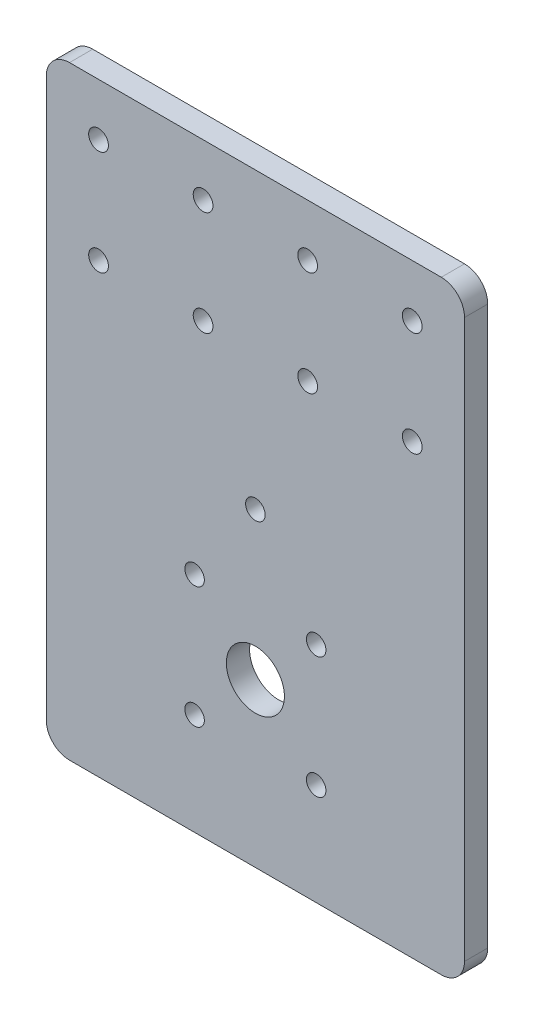
SolidWorks part; units mm, degrees
ref_plane "Front Plane" through (0, 0, 0) normal (0, 0, 1) x (1, 0, 0)
ref_plane "Top Plane" through (0, 0, 0) normal (0, 1, 0) x (1, 0, 0)
ref_plane "Right Plane" through (0, 0, 0) normal (1, 0, 0) x (0, 0, -1)
sketch "Sketch1" plane through (0, 0, 0) normal (0, 0, 1) x (1, 0, 0)
  line L0 (0, 0) -> (37, 0) construction
  line L1 (0, 0) -> (26.163, 26.163) construction
  line L2 (0, 0) -> (0, 63.5) construction
  line L3 (-66.1167, 190) -> (94.9569, 190) construction
  line L4 (0, 0) -> (0, -70) construction
  line L7 (-80, -70) -> (80, -70)
  line L9 (90, -60) -> (90, 180)
  line L10 (80, 190) -> (-80, 190)
  line L11 (-90, 180) -> (-90, -60)
  line L12 (-80, 167.5) -> (80, 167.5) construction
  line L13 (-80, 122.5) -> (80, 122.5) construction
  line L14 (-67.5, 177.3414) -> (-67.5, 115.1625) construction
  circle A0 centre (0, 0) radius 37 construction
  circle A2 centre (26.163, 26.163) radius 4.2
  circle A3 centre (26.163, -26.163) radius 4.2
  circle A4 centre (-26.163, -26.163) radius 4.2
  circle A5 centre (-26.163, 26.163) radius 4.2
  circle A6 centre (0, 63.5) radius 4.2
  arc A7 (90, -60) -> (80, -70) centre (80, -60) cw
  arc A8 (-80, -70) -> (-90, -60) centre (-80, -60) cw
  arc A9 (-90, 180) -> (-80, 190) centre (-80, 180) cw
  arc A10 (80, 190) -> (90, 180) centre (80, 180) cw
  circle A11 centre (-67.5, 167.5) radius 4.25
  circle A12 centre (-67.5, 122.5) radius 4.25
  circle A13 centre (-22.5, 122.5) radius 4.25
  circle A14 centre (-22.5, 167.5) radius 4.25
  circle A15 centre (22.5, 122.5) radius 4.25
  circle A16 centre (22.5, 167.5) radius 4.25
  circle A17 centre (67.5, 122.5) radius 4.25
  circle A18 centre (67.5, 167.5) radius 4.25
  circle A20 centre (0, 0) radius 12.5
  point P15 (0, 0)
  point P17 (18.5, 0)
  point P25 (90, -70)
  point P28 (-90, -70)
  point P33 (90, 190)
  dimension "D1" = 74
  dimension "D2" = 45
  dimension "D3" = 4
  dimension "D5" = 190
  dimension "D6" = 180
  dimension "D8" = 10
  dimension "D12" = 4
  dimension "D4" = 63.5
  dimension "D7" = 70
  dimension "D9" = 22.5
  dimension "D10" = 67.5
  dimension "D11" = 22.5
extrude "Boss-Extrude1" add sketch "Sketch1" along normal blind 10
